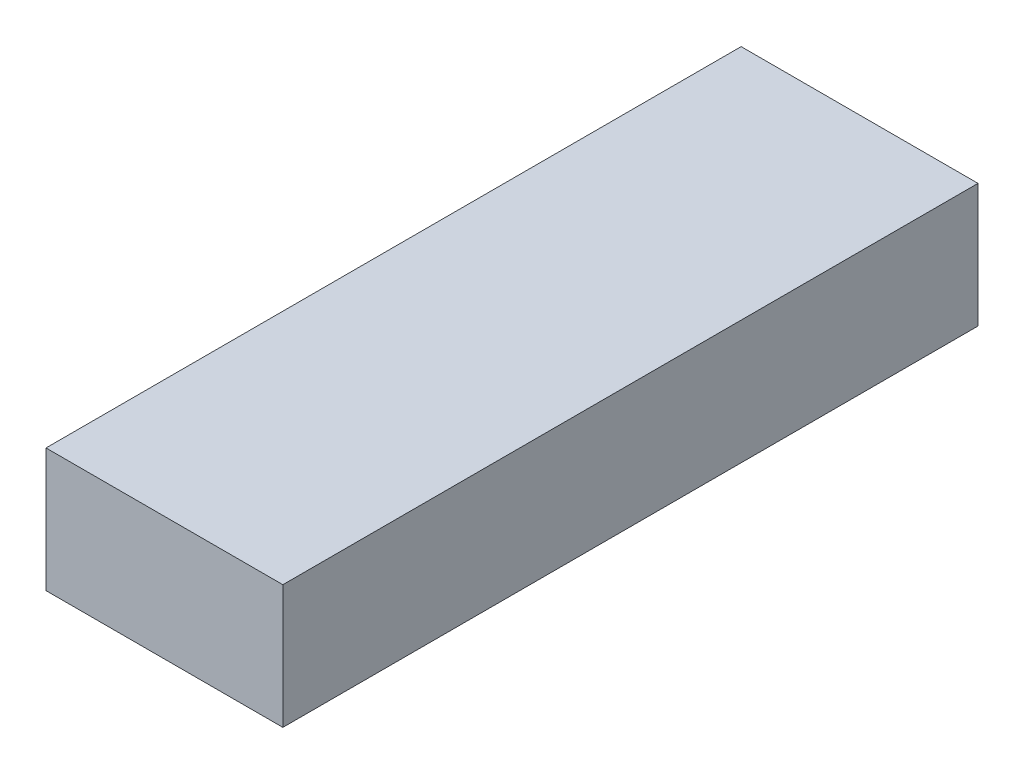
SolidWorks part; units mm, degrees
ref_plane "Front Plane" through (0, 0, 0) normal (0, 0, 1) x (1, 0, 0)
ref_plane "Top Plane" through (0, 0, 0) normal (0, 1, 0) x (1, 0, 0)
ref_plane "Right Plane" through (0, 0, 0) normal (1, 0, 0) x (0, 0, -1)
sketch "Sketch1" plane through (0, 0, 0) normal (0, 1, 0) x (1, 0, 0)
  line L1 (0, 0) -> (46, 0)
  line L2 (0, 0) -> (0, 135)
  line L3 (0, 135) -> (46, 135)
  line L4 (46, 0) -> (46, 135)
  dimension "D1" = 46
  dimension "D2" = 135
extrude "Boss-Extrude1" add sketch "Sketch1" along normal blind 24 contours L2 L3 L4 L1
